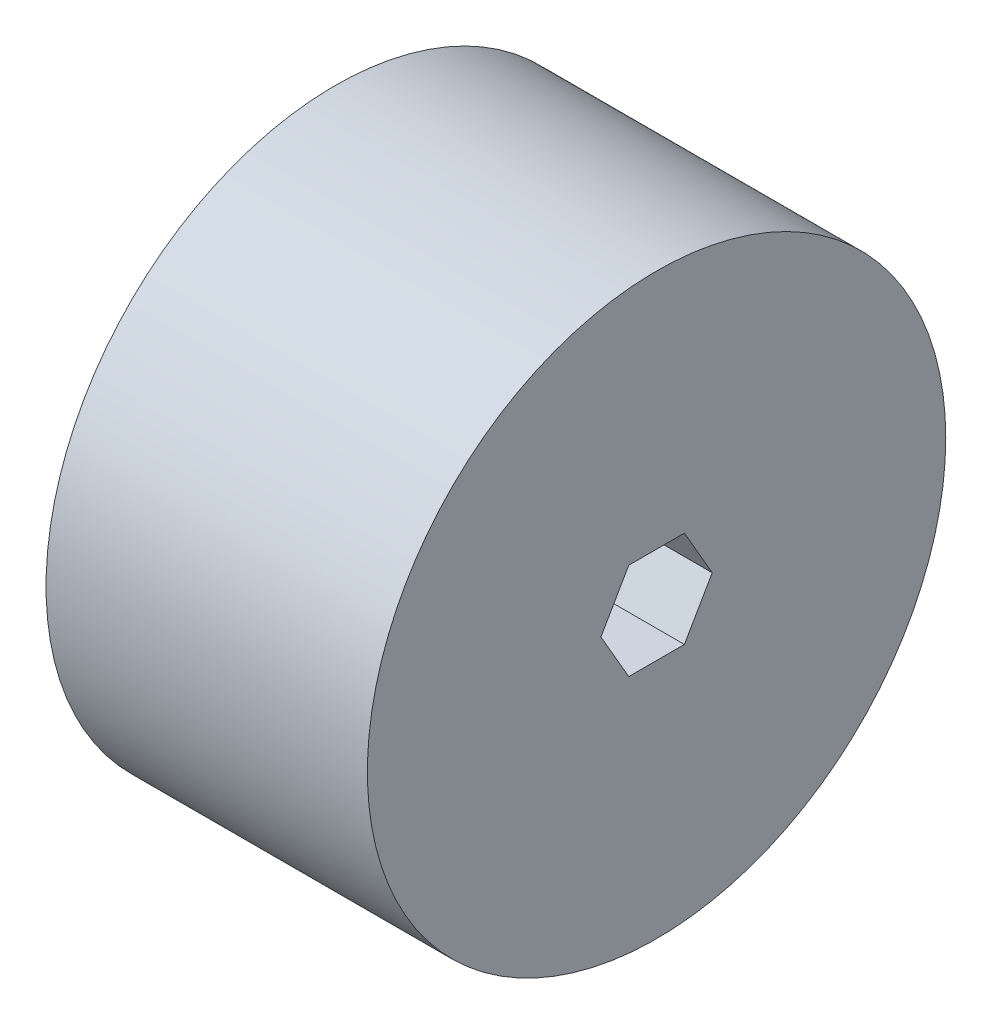
SolidWorks part; units mm, degrees
material "Brass"
ref_plane "Front" through (0, 0, 0) normal (0, 0, 1) x (1, 0, 0)
ref_plane "Top" through (0, 0, 0) normal (0, 1, 0) x (1, 0, 0)
ref_plane "Right" through (0, 0, 0) normal (1, 0, 0) x (0, 0, -1)
sketch "Sketch1" plane through (0, 0, 0) normal (1, 0, 0) x (0, 0, -1)
  circle A0 centre (0, 0) radius 28.575
  dimension "D1" = 57.15
extrude "Boss-Extrude1" add sketch "Sketch1" along normal blind 31.75 contours A0
sketch "Sketch2" plane through (31.75, 0, 0) normal (1, 0, 0) x (0, 0, -1)
  line L1 (2.7496, -4.7625) -> (5.4993, 0)
  line L2 (5.4993, 0) -> (2.7496, 4.7625)
  line L3 (2.7496, 4.7625) -> (-2.7496, 4.7625)
  line L4 (-2.7496, 4.7625) -> (-5.4993, 0)
  line L5 (-5.4993, 0) -> (-2.7496, -4.7625)
  line L6 (-2.7496, -4.7625) -> (2.7496, -4.7625)
  circle A0 centre (0, 0) radius 4.7625 construction
  dimension "D1" = 9.525
extrude "Cut-Extrude1" cut sketch "Sketch2" against normal through all contours L4 L5 L6 L1 L2 L3
